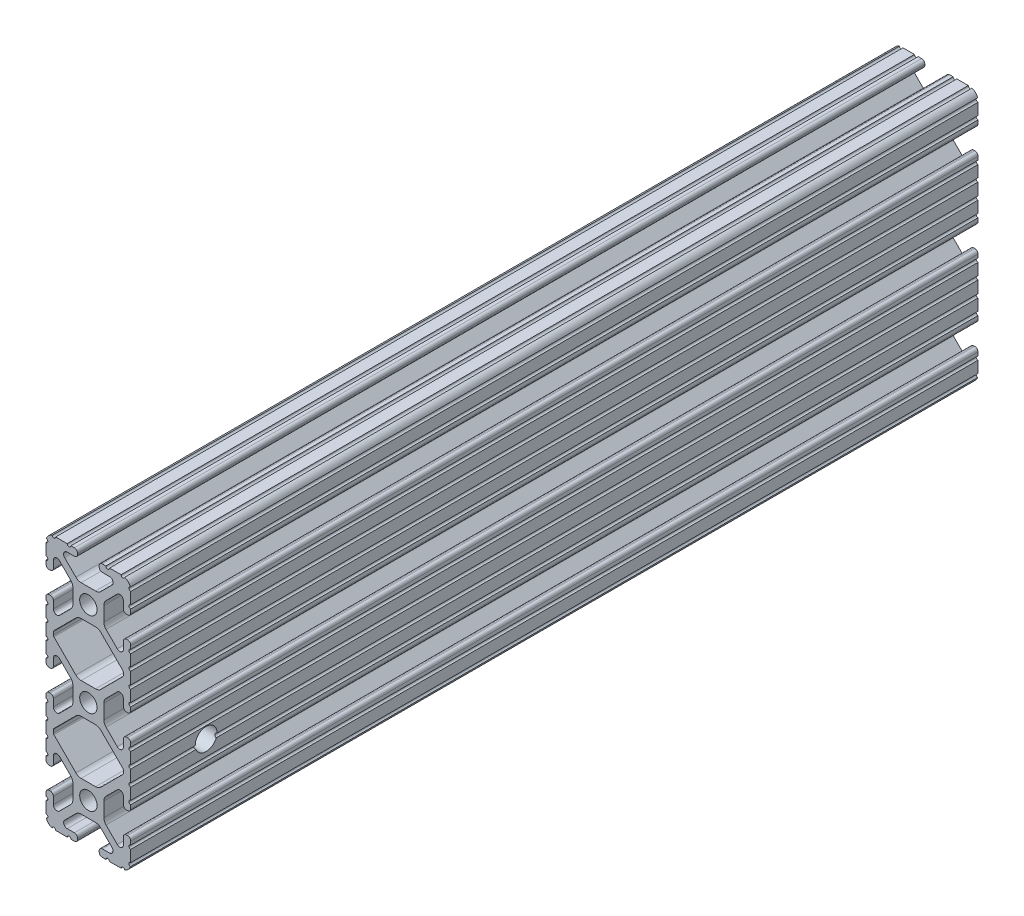
SolidWorks part; units mm, degrees
material "6061-T6 (SS)"
ref_plane "Front Plane" through (0, 0, 0) normal (0, 0, 1) x (1, 0, 0)
ref_plane "Top Plane" through (0, 0, 0) normal (0, 1, 0) x (1, 0, 0)
ref_plane "Right Plane" through (0, 0, 0) normal (1, 0, 0) x (0, 0, -1)
sketch "Sketch2" plane through (0, 0, 0) normal (0, 0, 1) x (1, 0, 0)
  line L0 (0, 38.1) -> (0, -38.1) construction
  line L1 (-12.7, 0) -> (12.7, 0) construction
  line L2 (3.2512, -38.1) -> (12.7, -38.1)
  line L3 (12.7, -38.1) -> (12.7, -28.6512)
  line L4 (3.2512, -38.1) -> (3.2512, -35.8902)
  line L5 (3.2512, -35.8902) -> (8.9276, -35.8902)
  line L6 (8.9276, -35.8902) -> (3.0856, -30.0482)
  line L7 (0, -25.4) -> (12.7, -38.1) construction
  line L8 (12.7, -28.6512) -> (10.4902, -28.6512)
  line L9 (10.4902, -28.6512) -> (10.4902, -34.3276)
  line L10 (10.4902, -34.3276) -> (4.6482, -28.4856)
  circle A0 centre (0, -25.4) radius 2.6035
  arc A1 (6.3485, -35.8902) -> (7.1039, -34.0665) centre (6.3485, -34.8219) ccw construction
  point P8 (0, -30.0482)
  dimension "Center Hole Diameter" = 5.207
  dimension "Rail Height" = 76.2
  dimension "Rail Width" = 25.4
  dimension "T-Slot Width" = 6.5024
  dimension "Slot Inner Width" = 14.8336
  dimension "Thickness" = 2.2098
  dimension "Slot Depth" = 5.842
  dimension "D1" = 2.2098
  dimension "D2" = 50.8
sketch "Sketch3" plane through (0, 0, 0) normal (1, 0, 0) x (0, 0, -1)
  line L0 (-152.4, -38.1) -> (152.4, -38.1) construction
  line L1 (-127, 0) -> (127, 0) construction
  dimension "D1" = 25.4
  dimension "Length" = 304.8
sketch "Sketch4" plane through (0, 0, 0) normal (0, 0, 1) x (1, 0, 0)
  line L0 (4.1904, -38.1) -> (10.1173, -38.1)
  line L1 (3.2512, -38.1) -> (12.7, -38.1) construction
  line L2 (3.2512, -38.1) -> (3.2512, -35.8902) construction
  line L3 (3.2512, -35.8902) -> (8.9276, -35.8902) construction
  line L4 (3.2512, -36.8294) -> (3.2512, -37.1608)
  line L5 (4.1904, -35.8902) -> (6.3485, -35.8902)
  line L6 (0, -30.0482) -> (2.164, -30.0482)
  line L7 (8.9276, -35.8902) -> (3.0856, -30.0482) construction
  line L8 (3.7373, -30.6999) -> (7.1039, -34.0665)
  line L9 (12.7, -38.1) -> (12.7, -28.6512) construction
  line L10 (10.4902, -34.3276) -> (4.6482, -28.4856) construction
  line L11 (10.4902, -28.6512) -> (10.4902, -34.3276) construction
  line L12 (10.4902, -31.7485) -> (10.4902, -29.5904)
  line L13 (12.7, -28.6512) -> (10.4902, -28.6512) construction
  line L14 (11.4294, -28.6512) -> (11.7608, -28.6512)
  line L15 (12.7, -29.5904) -> (12.7, -35.5173)
  line L16 (8.6665, -32.5039) -> (5.2999, -29.1373)
  line L17 (4.6482, -25.4) -> (4.6482, -27.564)
  line L19 (0, -30.0482) -> (0, -28.0035)
  line L20 (0, 38.1) -> (0, -38.1) construction
  line L21 (4.6482, -25.4) -> (2.6035, -25.4)
  arc A0 (3.2512, -37.1608) -> (4.1904, -38.1) centre (4.1904, -37.1608) ccw
  circle A1 centre (0, -25.4) radius 2.6035 construction
  arc A2 (3.2512, -36.8294) -> (4.1904, -35.8902) centre (4.1904, -36.8294) cw
  arc A3 (6.3485, -35.8902) -> (7.1039, -34.0665) centre (6.3485, -34.8219) ccw
  arc A4 (2.164, -30.0482) -> (3.7373, -30.6999) centre (2.164, -32.2732) cw
  arc A5 (10.1173, -38.1) -> (12.7, -35.5173) centre (10.1173, -35.5173) ccw
  arc A6 (8.6665, -32.5039) -> (10.4902, -31.7485) centre (9.4219, -31.7485) ccw
  arc A7 (10.4902, -29.5904) -> (11.4294, -28.6512) centre (11.4294, -29.5904) cw
  arc A8 (11.7608, -28.6512) -> (12.7, -29.5904) centre (11.7608, -29.5904) cw
  arc A9 (5.2999, -29.1373) -> (4.6482, -27.564) centre (6.8732, -27.564) cw
  arc A11 (0, -28.0035) -> (2.6035, -25.4) centre (0, -25.4) ccw
  dimension "D1" = 2.5827
  dimension "D2" = 2.225
  dimension "D3" = 0.9392
extrude "Boss-Extrude1" add sketch "Sketch4" along normal mid plane 254
sketch "Sketch5" plane through (0, 0, 0) normal (0, 0, 1) x (1, 0, 0)
  line L0 (3.2512, -38.1) -> (12.7, -38.1) construction
  line L1 (4.1904, -35.8902) -> (6.3485, -35.8902) construction
  line L3 (0, -25.4) -> (12.7, -38.1) construction
  line L4 (6.3485, -35.8902) -> (6.3485, -38.1) construction
  line L5 (8.9276, -35.8902) -> (3.0856, -30.0482) construction
  circle A0 centre (10.3562, -38.1) radius 0.5524
  circle A1 centre (5.796, -38.1) radius 0.5524
  circle A2 centre (12.7, -35.7562) radius 0.5525
  circle A3 centre (12.7, -31.196) radius 0.5525
  point P10 (5.2694, -35.8902)
  point P12 (9.4219, -31.7485)
  dimension "D1" = 1.1049
extrude "Cut-Extrude1" cut sketch "Sketch5" against normal through all both and the other way through all
mirror "Mirror1" about plane through (4.6482, -25.4, 127) normal (0, -1, 0) of bodies 137 134
sketch "Sketch6" plane through (0, 0, 0) normal (0, 0, 1) x (1, 0, 0)
  line L0 (12.7, -14.4914) -> (12.7, -12.7)
  line L1 (12.7, -12.7) -> (9.8037, -12.7)
  line L3 (9.8037, -12.7) -> (9.8037, -15.5963)
  line L4 (9.8037, -15.5963) -> (12.7, -15.5963)
  line L5 (6.3485, -12.7) -> (9.8037, -12.7) construction
  circle A0 centre (12.7, -15.0438) radius 0.5525 construction
  arc A1 (12.7, -14.4914) -> (12.7, -15.5963) centre (12.7, -15.0438) ccw
  arc A4 (9.8037, -12.7) -> (10.8954, -12.82) centre (10.3562, -12.7) ccw construction
extrude "Boss-Extrude2" add sketch "Sketch6" along normal mid plane 254
sketch "Sketch7" plane through (0, 0, 0) normal (0, 0, 1) x (1, 0, 0)
  line L0 (5.4206, -18.4168) -> (10.3284, -13.509)
  line L1 (3.7373, -20.1001) -> (7.1039, -16.7335) construction
  line L2 (10.4902, -13.1184) -> (10.4902, -12.7)
  line L3 (0, -12.7) -> (10.4902, -12.7)
  line L5 (0, -12.7) -> (5.4206, -18.4168)
  line L7 (0, 38.1) -> (0, -38.1) construction
  line L8 (6.3485, -12.7) -> (12.7, -12.7) construction
  arc A0 (10.3284, -13.509) -> (10.4902, -13.1184) centre (9.9377, -13.1184) ccw
  arc A3 (12.7, -14.4914) -> (12.7, -15.5963) centre (12.7, -15.0438) ccw construction
extrude "Cut-Extrude2" cut sketch "Sketch7" against normal through all both and the other way through all
mirror "Mirror2" about plane through (4.1904, -12.7, 127) normal (0, -1, 0) of bodies 139 135
other "SurfaceCut1"
mirror "Mirror3" about plane through (0, 0, 0) normal (1, 0, 0) of bodies 142 136
mirror "Mirror4" about plane through (0, 0, 0) normal (0, 1, 0) of bodies 140
sketch "Sketch8" plane through (-12.7, 0, 0) normal (-1, 0, 0) x (0, 0, 1)
  circle A0 centre (104.4, -14.4) radius 3.2639
  dimension "D1" = 6.5278
extrude "Cut-Extrude3" cut sketch "Sketch8" against normal through all
equation "\"D1@Sketch2\"= \"Thickness@Sketch2\""
equation "\"D2@Sketch4\"=\"Slot Inner Width@Sketch2\"*0.15"
equation "\"D1@Sketch4\"=\"D3@Sketch4\"*2.75"
equation "\"D3@Sketch4\"=\"Thickness@Sketch2\"*0.425"
equation "\"D1@Sketch5\"= \"Thickness@Sketch2\" * 0.5"
equation "\"azimuth_horizontal_rail_length\"=(\"altitude_horizontal_rail_length\"+6in-0.29in)"
equation "\"azimuth_vertictal_rail_length\"=6in"
equation "\"wall_screw_clearance_diameter\"=4.3mm"
equation "\"altitude_horizontal_rail_length\"=10in"
equation "\"altitude_vertictal_rail_length\"=12in"
equation "\"azimuth_vertictal_rail_length_short\"=(\"altitude_vertictal_rail_length\"-5in)"
equation "\"azimuth_vertictal_rail_length_long\"=(\"azimuth_vertictal_rail_length_short\"+4in)"
equation "\"table_length\"=72in"
equation "\"table_width\"=25in"
equation "\"table_thickness\"=1.75in"
equation "\"azimuth_mounting_hole_distance\"=9in"
equation "\"table_frame_vertical_length\"=12.5in"
equation "\"table_frame_diagonal_length\"=17.5in"
equation "\"linear_horizontal_rail_length\"=12in"
equation "\"linear_vertictal_rail_length\"=10in"
equation "\"D1@Boss-Extrude1\"=\"linear_vertictal_rail_length\""
equation "\"D1@Boss-Extrude2\"=\"linear_vertictal_rail_length\""
